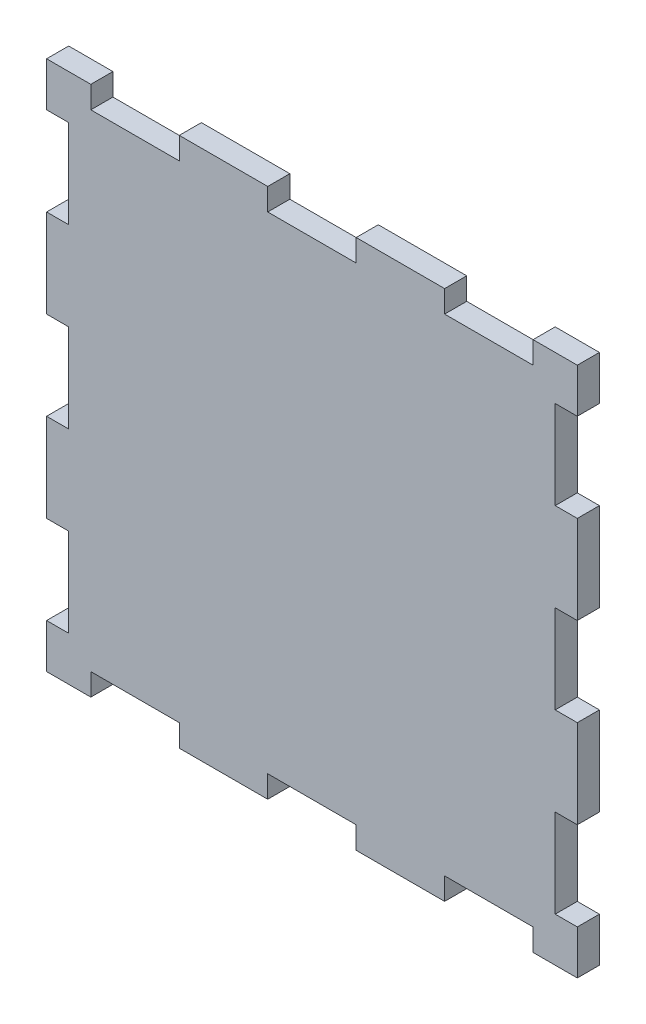
SolidWorks part; units mm, degrees
ref_plane "Front Plane" through (0, 0, 0) normal (0, 0, 1) x (1, 0, 0)
ref_plane "Top Plane" through (0, 0, 0) normal (0, 1, 0) x (1, 0, 0)
ref_plane "Right Plane" through (0, 0, 0) normal (1, 0, 0) x (0, 0, -1)
sketch "Sketch1" plane through (0, 0, 0) normal (0, 0, 1) x (1, 0, 0)
  line L1 (0, 0) -> (76.2, 0)
  line L2 (0, 0) -> (0, 76.2)
  line L3 (0, 76.2) -> (76.2, 76.2)
  line L4 (76.2, 0) -> (76.2, 76.2)
  dimension "D1" = 76.2
  dimension "D2" = 76.2
extrude "Extrude1" add sketch "Sketch1" along normal blind 3.175
sketch "Sketch3" plane through (0, 0, 3.175) normal (0, 0, 1) x (1, 0, 0)
  line L0 (76.2, 0) -> (76.2, 76.2) construction
  line L1 (76.2, 69.85) -> (73.025, 69.85)
  line L2 (76.2, 69.85) -> (76.2, 57.15)
  line L3 (76.2, 57.15) -> (73.025, 57.15)
  line L4 (73.025, 69.85) -> (73.025, 57.15)
  line L5 (76.2, 76.2) -> (0, 76.2) construction
  dimension "D1" = 3.175
  dimension "D2" = 12.7
  dimension "D3" = 6.35
extrude "Cut-Extrude1" cut sketch "Sketch3" against normal blind 3.175
pattern_linear "LPattern1" count 3 spacing 25.4 along (0, -1, 0) count 2 spacing 73.025 along (-1, 0, 0) of "Cut-Extrude1"
sketch "Sketch4" plane through (0, 0, 3.175) normal (0, 0, 1) x (1, 0, 0)
  line L0 (76.2, 76.2) -> (0, 76.2) construction
  line L1 (69.85, 76.2) -> (57.15, 76.2)
  line L2 (69.85, 76.2) -> (69.85, 73.025)
  line L3 (69.85, 73.025) -> (57.15, 73.025)
  line L4 (57.15, 76.2) -> (57.15, 73.025)
  dimension "D1" = 12.7
  dimension "D2" = 3.175
  dimension "D3" = 6.35
extrude "Cut-Extrude2" cut sketch "Sketch4" against normal blind 3.175
pattern_linear "LPattern2" count 3 spacing 25.4 along (-1, 0, 0) count 2 spacing 73.025 along (0, -1, 0) of "Cut-Extrude2"
